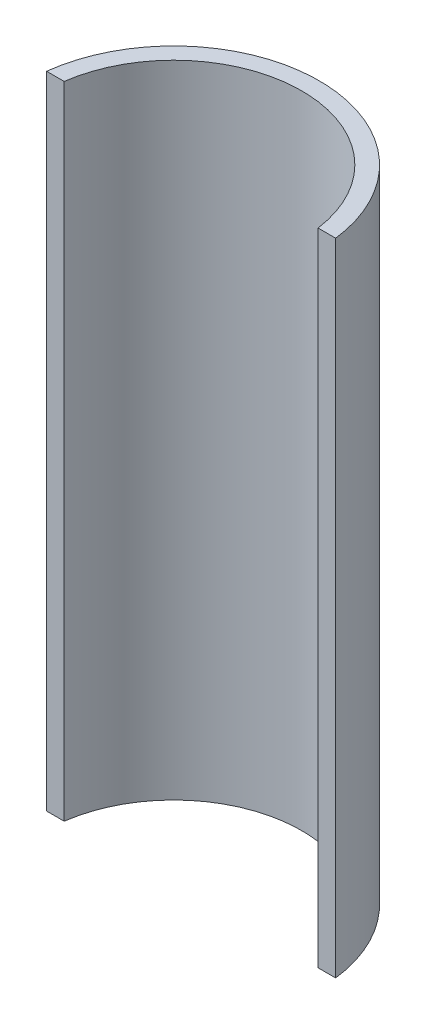
SolidWorks part; units mm, degrees
ref_plane "Front Plane" through (0, 0, 0) normal (0, 0, 1) x (1, 0, 0)
ref_plane "Top Plane" through (0, 0, 0) normal (0, 1, 0) x (1, 0, 0)
ref_plane "Right Plane" through (0, 0, 0) normal (1, 0, 0) x (0, 0, -1)
sketch "Sketch1" plane through (0, 0, 0) normal (0, 1, 0) x (1, 0, 0)
  line L0 (-24.8193, 3) -> (-21.7945, 3)
  line L1 (-24.8193, -3) -> (-21.7945, -3)
  line L2 (21.7945, 3) -> (24.8193, 3)
  line L3 (21.7945, -3) -> (24.8193, -3)
  arc A0 (-24.8193, -3) -> (24.8193, -3) centre (0, 0) ccw
  arc A1 (-21.7945, -3) -> (21.7945, -3) centre (0, 0) ccw
  arc A2 (21.7945, 3) -> (-21.7945, 3) centre (0, 0) ccw
  arc A3 (24.8193, 3) -> (-24.8193, 3) centre (0, 0) ccw
  dimension "D3" = 22
  dimension "D4" = 25
  dimension "D1" = 6
  dimension "D2" = 3
extrude "Boss-Extrude1" add sketch "Sketch1" along normal mid plane 110 contours A2 L0 A3 L2
sketch "Sketch2" plane through (0, 0, 0) normal (0, 0, 1) x (1, 0, 0)
  line L2 (-10, -20) -> (-10, 20)
  line L4 (10, -20) -> (10, 20)
  line L5 (-10, -20) -> (10, 20) construction
  line L6 (-10, 20) -> (10, -20) construction
  arc A0 (10, 20) -> (-10, 20) centre (0, 20) ccw
  arc A1 (-10, -20) -> (10, -20) centre (0, -20) ccw
  point P11 (0, 0)
  dimension "D3" = 10
  dimension "D1" = 20
  dimension "D2" = 40
extrude "Cut-Extrude1" [suppressed] cut sketch "Sketch2" along normal blind 80
